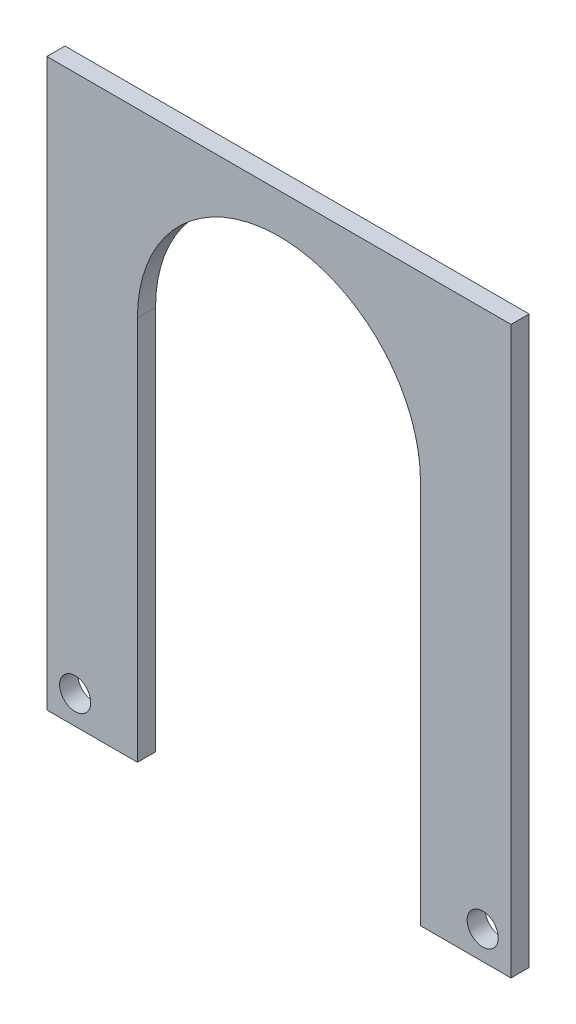
SolidWorks part; units mm, degrees
material "AISI 304"
ref_plane "Front Plane" through (0, 0, 0) normal (0, 0, 1) x (1, 0, 0)
ref_plane "Top Plane" through (0, 0, 0) normal (0, 1, 0) x (1, 0, 0)
ref_plane "Right Plane" through (0, 0, 0) normal (1, 0, 0) x (0, 0, -1)
sketch "Sketch1" plane through (0, 0, 0) normal (0, 0, 1) x (1, 0, 0)
  line L0 (-75, 80) -> (75, -80) construction
  line L1 (-75, 80) -> (75, 80)
  line L2 (-75, 80) -> (-75, -80)
  line L3 (-75, -80) -> (75, -80)
  line L4 (75, 80) -> (75, -80)
  point P0 (0, 0)
  point P6 (0, 0)
  dimension "D1" = 150
  dimension "D2" = 160
extrude "Boss-Extrude1" add sketch "Sketch1" along normal blind 3.2
sketch "Sketch2" plane through (0, 0, 3.2) normal (0, 0, 1) x (1, 0, 0)
  line L0 (0, -12) -> (0, -47.5) construction
  line L1 (-25, -12) -> (-25, -80)
  line L2 (25, -12) -> (25, -80)
  line L3 (-75, -80) -> (75, -80) construction
  line L4 (-25, -80) -> (25, -80)
  arc A1 (-25, -12) -> (25, -12) centre (0, -12) cw
  dimension "D1" = 35.5
  dimension "D3" = 25
  dimension "D4" = 68
extrude "Cut-Extrude1" cut sketch "Sketch2" against normal up to next
sketch "Sketch3" plane through (0, 0, 3.2) normal (0, 0, 1) x (1, 0, 0)
  line L0 (-41, 20) -> (-41, -80)
  line L1 (-75, -80) -> (-25, -80) construction
  line L2 (-41, -80) -> (-75, -80)
  line L3 (-75, -80) -> (-75, 80)
  line L4 (-75, 80) -> (75, 80)
  line L5 (-41, 20) -> (41, 20)
  line L6 (75, 80) -> (75, -80)
  line L7 (25, -80) -> (75, -80) construction
  line L8 (41, -80) -> (41, 20)
  line L9 (75, -80) -> (41, -80)
  circle A0 centre (36, -75) radius 2.75 construction
  circle A1 centre (36, -75) radius 2.75
  circle A2 centre (-36, -75) radius 2.75 construction
  circle A3 centre (-36, -75) radius 2.75
  dimension "D1" = 82
  dimension "D2" = 100
extrude "Cut-Extrude2" cut sketch "Sketch3" against normal up to next
